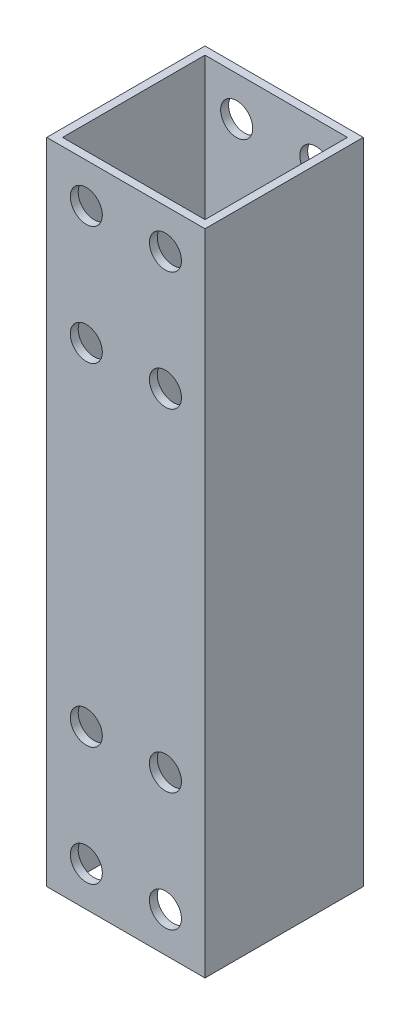
SolidWorks part; units mm, degrees
material "6061 合金"
ref_plane "前视基准面" through (0, 0, 0) normal (0, 0, 1) x (1, 0, 0)
ref_plane "上视基准面" through (0, 0, 0) normal (0, 1, 0) x (1, 0, 0)
ref_plane "右视基准面" through (0, 0, 0) normal (1, 0, 0) x (0, 0, -1)
sketch "草图1" plane through (0, 0, 0) normal (0, 1, 0) x (1, 0, 0)
  line L0 (-9, 9) -> (9, 9)
  line L1 (-10, 10) -> (10, 10)
  line L2 (-10, 10) -> (-10, -10)
  line L3 (-10, -10) -> (10, -10)
  line L4 (10, 10) -> (10, -10)
  line L5 (0, -10) -> (0, 10) construction
  line L6 (-10, 0) -> (10, 0) construction
  line L7 (9, 9) -> (9, -9)
  line L8 (-9, -9) -> (9, -9)
  line L9 (-9, 9) -> (-9, -9)
  point P0 (0, 0)
  dimension "D1" = 20
  dimension "D2" = 20
  dimension "D3" = 1
extrude "凸台-拉伸1" add sketch "草图1" along normal blind 82
sketch "草图2" plane through (0, 0, 10) normal (0, 0, 1) x (1, 0, 0)
  line L0 (-10, 0) -> (10, 0) construction
  line L1 (-5, 20) -> (5, 20) construction
  line L2 (-5, 20) -> (-5, 5) construction
  line L3 (-5, 5) -> (5, 5) construction
  line L4 (5, 20) -> (5, 5) construction
  line L5 (0, 5) -> (0, 20) construction
  line L6 (-5, 12.5) -> (5, 12.5) construction
  line L7 (-10, 82) -> (10, 82) construction
  line L8 (-5, 77) -> (5, 77) construction
  line L9 (-5, 77) -> (-5, 62) construction
  line L10 (-5, 62) -> (5, 62) construction
  line L11 (5, 77) -> (5, 62) construction
  line L12 (0, 62) -> (0, 77) construction
  line L13 (-5, 69.5) -> (5, 69.5) construction
  circle A0 centre (-5, 5) radius 2.025
  circle A1 centre (-5, 20) radius 2.025
  circle A2 centre (5, 20) radius 2.025
  circle A3 centre (5, 5) radius 2.025
  circle A4 centre (5, 77) radius 2.025
  circle A7 centre (-5, 77) radius 2.025
  circle A8 centre (-5, 62) radius 2.025
  circle A9 centre (5, 62) radius 2.025
  point P0 (0, 12.5)
  point P10 (0, 69.5)
  dimension "D5" = 15
  dimension "D9" = 4.05
  dimension "D1" = 5
  dimension "D2" = 15
  dimension "D3" = 10
  dimension "D4" = 0
  dimension "D6" = 0
  dimension "D7" = 10
  dimension "D8" = 5
extrude "切除-拉伸1" cut sketch "草图2" against normal through all
